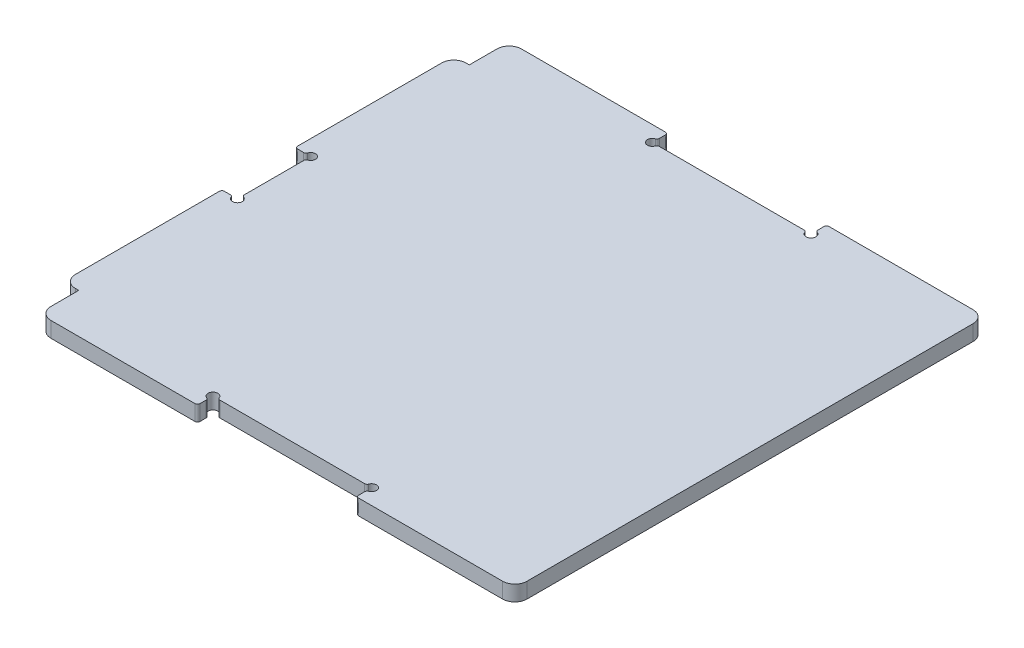
SolidWorks part; units mm, degrees
material "Pine"
ref_plane "Front Plane" through (0, 0, 0) normal (0, 0, 1) x (1, 0, 0)
ref_plane "Top Plane" through (0, 0, 0) normal (0, 1, 0) x (1, 0, 0)
ref_plane "Right Plane" through (0, 0, 0) normal (1, 0, 0) x (0, 0, -1)
sketch "Sketch1" plane through (0, 0, 0) normal (0, 1, 0) x (1, 0, 0)
  line L0 (0, 0) -> (195, 0)
  line L1 (0, 0) -> (0, 180)
  line L2 (195, 0) -> (195, 180)
  line L3 (0, 180) -> (195, 180)
  dimension "D1" = 195
  dimension "D2" = 180
extrude "Boss-Extrude1" add sketch "Sketch1" along normal mid plane 6.35
ref_plane "Plane1" through (0, 0, -90) normal (0, 0, 1) x (1, 0, 0)
ref_plane "Plane2" through (97.5, 0, 0) normal (1, 0, 0) x (0, 0, -1)
sketch "Sketch2" plane through (0, 3.175, 0) normal (0, 1, 0) x (1, 0, 0)
  line L0 (195, 0) -> (130, 0)
  line L1 (195, 0) -> (195, -6.35)
  line L2 (130, 0) -> (130, -6.35)
  line L3 (195, -6.35) -> (130, -6.35)
  line L4 (0, 0) -> (195, 0) construction
  dimension "D1" = 6.35
  dimension "D2" = 65
extrude "Boss-Extrude2" add sketch "Sketch2" against normal up to surface (6.35 mm away) up to face at (97.5, -3.175, -90)
pattern_linear "LPattern1" count 2 spacing 130 along (-1, 0, 0) of "Boss-Extrude2"
mirror "Mirror1" about plane through (0, 0, -90) normal (0, 0, 1) of "LPattern1", "Boss-Extrude2"
sketch "Sketch3" plane through (0, 3.175, 0) normal (0, 1, 0) x (1, 0, 0)
  line L0 (0, 170) -> (0, 105)
  line L1 (0, 170) -> (-6.35, 170)
  line L2 (0, 105) -> (-6.35, 105)
  line L3 (-6.35, 170) -> (-6.35, 105)
  line L4 (0, 186.35) -> (0, -6.35) construction
  line L5 (0, 75) -> (0, 10)
  line L6 (0, 75) -> (-6.35, 75)
  line L7 (0, 10) -> (-6.35, 10)
  line L8 (-6.35, 75) -> (-6.35, 10)
  line L9 (195, 90) -> (0, 90) construction
  line L10 (195, -6.35) -> (195, 186.35) construction
  line L11 (0, 105) -> (0, 90) construction
  line L12 (0, 90) -> (0, 75) construction
  dimension "D1" = 6.35
  dimension "D2" = 65
  dimension "D3" = 30
extrude "Boss-Extrude3" add sketch "Sketch3" against normal up to surface (6.35 mm away)
sketch "Sketch4" plane through (0, 3.175, 0) normal (0, 1, 0) x (1, 0, 0)
  circle A0 centre (65, 0) radius 2
  circle A1 centre (130, 0) radius 2
  dimension "D1" = 4
extrude "Cut-Extrude1" cut sketch "Sketch4" against normal through all
fillet "Fillet1" radius 1 2 edges at (130, 0, 6.35) (65, 0, 6.35)
sketch "Sketch5" plane through (0, 3.175, 0) normal (0, 1, 0) x (1, 0, 0)
  line L0 (130, -2) -> (130, -5.35) construction
  line L1 (67, 0) -> (128, 0) construction
  line L2 (65, -5.35) -> (65, -2) construction
  line L3 (130, -2.8284) -> (130, -5.35)
  line L4 (67.8284, 0) -> (127.1716, 0)
  line L5 (65, -5.35) -> (65, -2.8284)
  line L6 (131, -6.35) -> (64, -6.35)
  arc A0 (130, -5.35) -> (131, -6.35) centre (131, -5.35) ccw construction
  arc A1 (130, -2) -> (128, 0) centre (130, 0) ccw construction
  arc A2 (67, 0) -> (65, -2) centre (65, 0) ccw construction
  arc A3 (64, -6.35) -> (65, -5.35) centre (64, -5.35) ccw construction
  arc A4 (130, -5.35) -> (131, -6.35) centre (131, -5.35) ccw
  arc A5 (130.6667, -1.8856) -> (128.1144, 0.6667) centre (130, 0) ccw
  arc A6 (66.8856, 0.6667) -> (64.3333, -1.8856) centre (65, 0) ccw
  arc A7 (64, -6.35) -> (65, -5.35) centre (64, -5.35) ccw
  arc A8 (130, -2.8284) -> (130.6667, -1.8856) centre (131, -2.8284) cw
  arc A9 (128.1144, 0.6667) -> (127.1716, 0) centre (127.1716, 1) cw
  arc A10 (67.8284, 0) -> (66.8856, 0.6667) centre (67.8284, 1) cw
  arc A11 (64.3333, -1.8856) -> (65, -2.8284) centre (64, -2.8284) cw
  dimension "D1" = 1
extrude "Cut-Extrude2" cut sketch "Sketch5" against normal through all
mirror "Mirror3" about plane through (0, 0, -90) normal (0, 0, 1) of "Cut-Extrude2"
sketch "Sketch6" plane through (0, 3.175, 0) normal (0, 1, 0) x (1, 0, 0)
  circle A0 centre (0, 105) radius 2
  circle A1 centre (0, 75) radius 2
  dimension "D1" = 4
extrude "Cut-Extrude3" cut sketch "Sketch6" against normal through all
fillet "Fillet2" radius 1 6 edges at (-6.35, 0, -75) (-2, 0, -75) (0, 0, -77) (0, 0, -103) (-2, 0, -105) (-6.35, 0, -105)
fillet "Fillet3" radius 5 6 edges at (195, 0, -186.35) (195, 0, 6.35) (-6.35, 0, -10) (-6.35, 0, -170) (0, 0, 6.35) (0, 0, -186.35)
